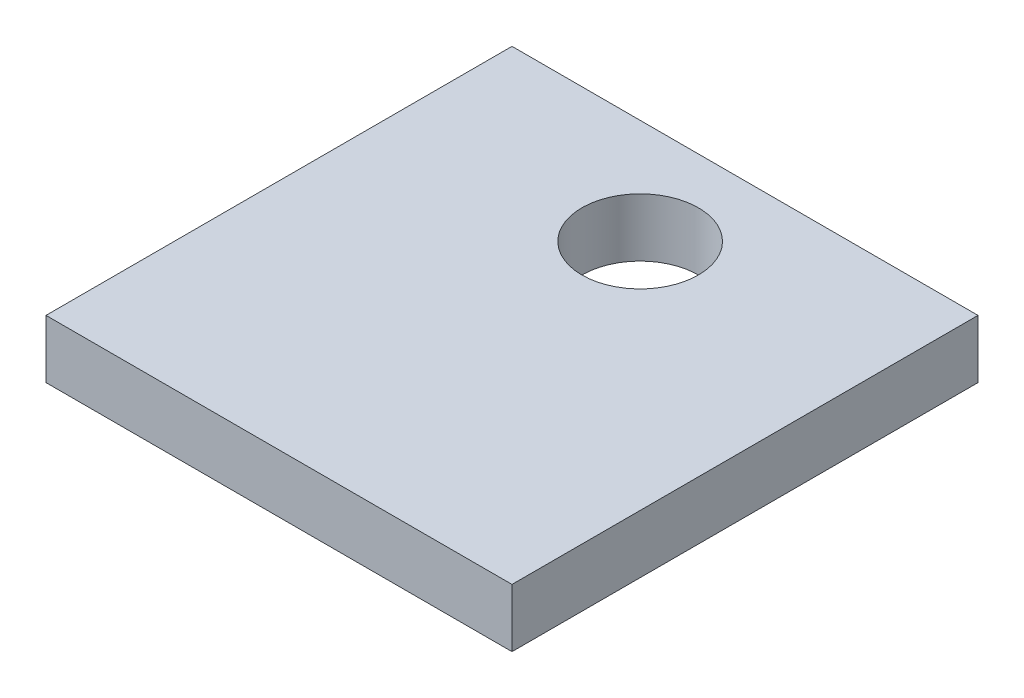
SolidWorks part; units mm, degrees
material "ALUMINIUM"
ref_plane "Front" through (0, 0, 0) normal (0, 0, 1) x (1, 0, 0)
ref_plane "Top" through (0, 0, 0) normal (0, 1, 0) x (1, 0, 0)
ref_plane "Right" through (0, 0, 0) normal (1, 0, 0) x (0, 0, -1)
sketch "Sketch1" plane through (0, 0, 0) normal (0, 1, 0) x (1, 0, 0)
  line L1 (40, 40) -> (-40, 40)
  line L2 (40, 40) -> (40, -40)
  line L3 (40, -40) -> (-40, -40)
  line L4 (-40, 40) -> (-40, -40)
  line L5 (40, 40) -> (-40, -40) construction
  line L6 (40, -40) -> (-40, 40) construction
  point P0 (0, 0)
  dimension "D1" = 80
  dimension "D2" = 80
extrude "Boss-Extrude1" add sketch "Sketch1" against normal mid plane 10
sketch "Sketch2" plane through (0, 5, 0) normal (0, 1, 0) x (1, 0, 0)
  line L0 (40, 40) -> (-40, 40) construction
  circle A0 centre (0, 22) radius 10
  dimension "D1" = 20
  dimension "D2" = 18
extrude "Cut-Extrude1" cut sketch "Sketch2" against normal through all
